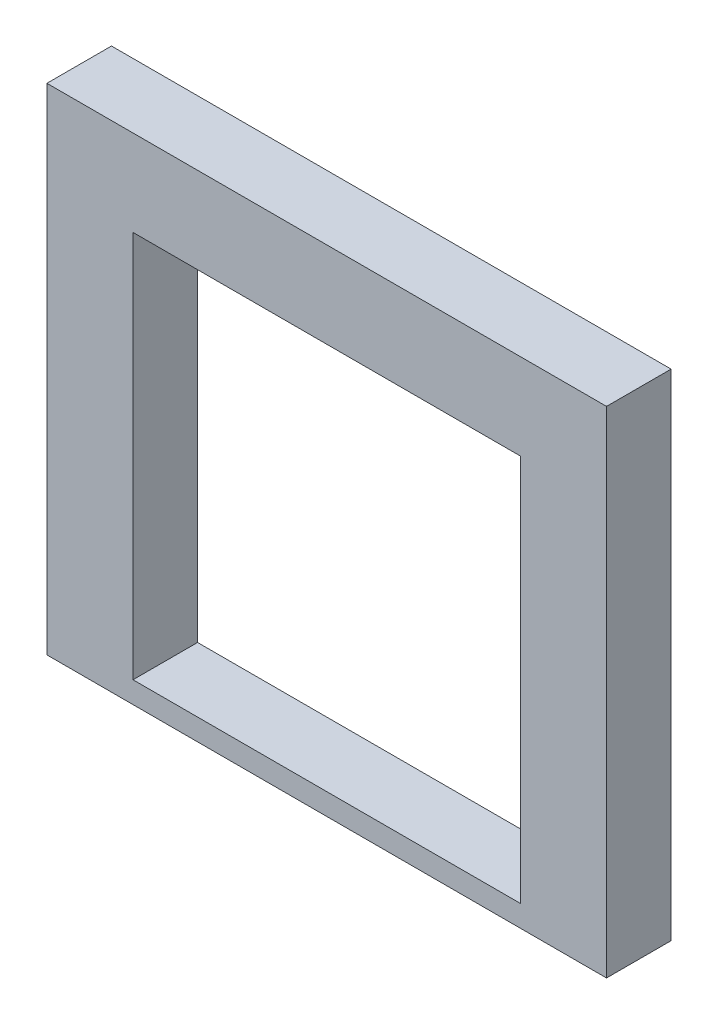
SolidWorks part; units mm, degrees
ref_plane "Front Plane" through (0, 0, 0) normal (0, 0, 1) x (1, 0, 0)
ref_plane "Top Plane" through (0, 0, 0) normal (0, 1, 0) x (1, 0, 0)
ref_plane "Right Plane" through (0, 0, 0) normal (1, 0, 0) x (0, 0, -1)
sketch "Sketch1" plane through (0, 0, 0) normal (0, 0, 1) x (1, 0, 0)
  line L1 (4.5, -4.5) -> (-4.5, -4.5)
  line L2 (4.5, -4.5) -> (4.5, 4.5)
  line L3 (4.5, 4.5) -> (-4.5, 4.5)
  line L4 (-4.5, -4.5) -> (-4.5, 4.5)
  line L5 (4.5, -4.5) -> (-4.5, 4.5) construction
  line L6 (4.5, 4.5) -> (-4.5, -4.5) construction
  line L7 (6.5, -5) -> (-6.5, -5)
  line L8 (6.5, -5) -> (6.5, 6.5)
  line L9 (6.5, 6.5) -> (-6.5, 6.5)
  line L10 (-6.5, -5) -> (-6.5, 6.5)
  point P0 (0, 0)
  point P6 (0, 0)
  dimension "D1" = 9
  dimension "D2" = 2
  dimension "D3" = 2
  dimension "D4" = 2
  dimension "D5" = 0.5
extrude "Boss-Extrude1" add sketch "Sketch1" along normal blind 1.5
